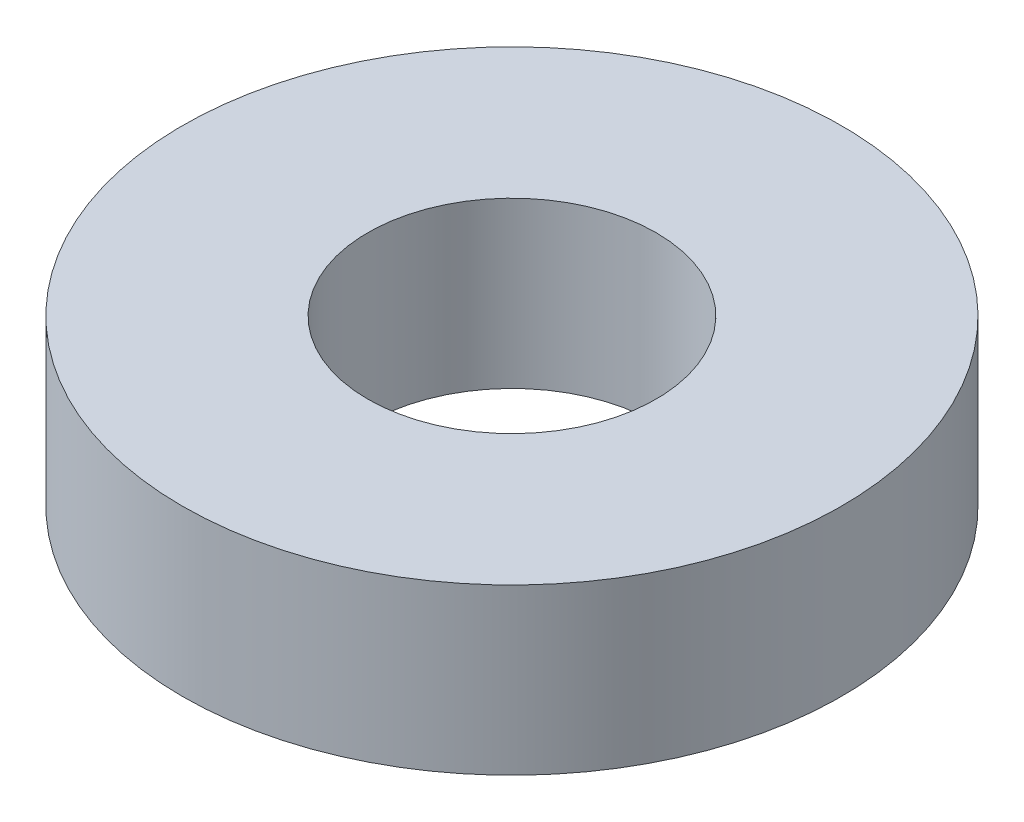
SolidWorks part; units mm, degrees
ref_plane "Front Plane" through (0, 0, 0) normal (0, 0, 1) x (1, 0, 0)
ref_plane "Top Plane" through (0, 0, 0) normal (0, 1, 0) x (1, 0, 0)
ref_plane "Right Plane" through (0, 0, 0) normal (1, 0, 0) x (0, 0, -1)
sketch "Sketch1" plane through (0, 0, 0) normal (0, 1, 0) x (1, 0, 0)
  circle A0 centre (0, 0) radius 1.75
  circle A1 centre (0, 0) radius 4
  dimension "D1" = 8
  dimension "D2" = 3.5
extrude "Boss-Extrude1" add sketch "Sketch1" along normal blind 2 contours A0 | A1
